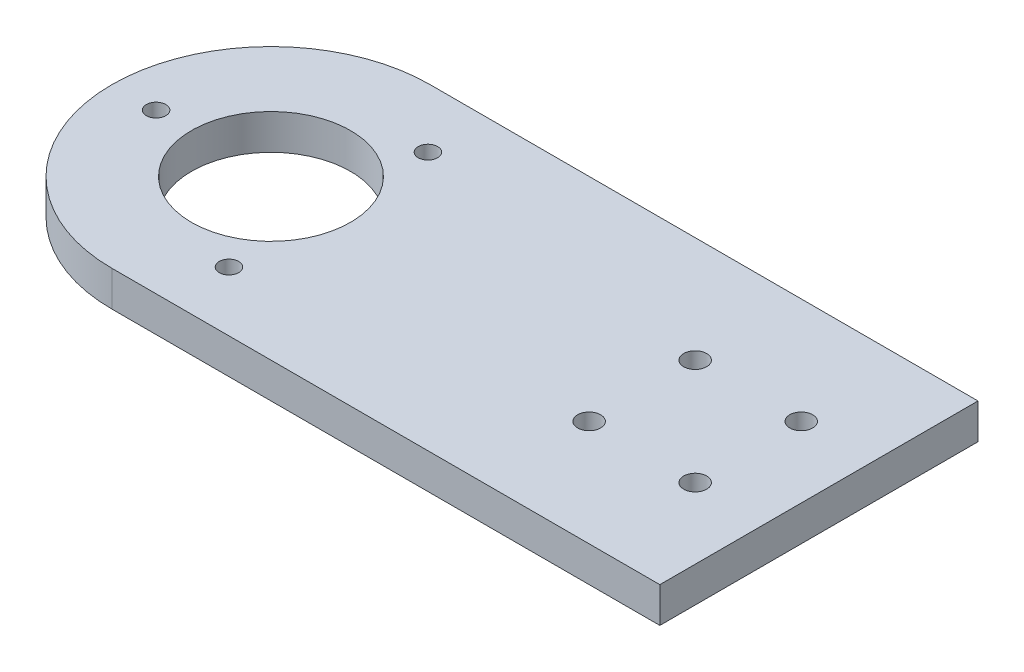
SolidWorks part; units mm, degrees
ref_plane "Front Plane" through (0, 0, 0) normal (0, 0, 1) x (1, 0, 0)
ref_plane "Top Plane" through (0, 0, 0) normal (0, 1, 0) x (1, 0, 0)
ref_plane "Right Plane" through (0, 0, 0) normal (1, 0, 0) x (0, 0, -1)
sketch "Sketch1" plane through (0, 0, 0) normal (0, 1, 0) x (1, 0, 0)
  line L0 (-55, 45) -> (100, 45)
  line L1 (-100, -45) -> (100, -45) construction
  line L2 (-100, -45) -> (-100, 45) construction
  line L3 (-100, 45) -> (100, 45) construction
  line L4 (100, -45) -> (100, 45) construction
  line L5 (0, 45) -> (0, -45) construction
  line L6 (-100, 0) -> (100, 0) construction
  line L7 (100, 45) -> (100, -45)
  line L8 (100, -45) -> (-55, -45)
  arc A1 (-55, 45) -> (-54.7588, -44.9994) centre (-55, 0) ccw
  point P0 (0, 0)
  dimension "D1" = 90
  dimension "D2" = 200
extrude "Boss-Extrude1" add sketch "Sketch1" along normal blind 10
sketch "Sketch2" plane through (0, 10, 0) normal (0, 1, 0) x (1, 0, 0)
  circle A0 centre (-55, 0) radius 32.5 construction
  circle A1 centre (-87.5, 0) radius 2.75
  circle A2 centre (-38.75, 28.1458) radius 2.75
  circle A3 centre (-38.75, -28.1458) radius 2.75
  circle A4 centre (-55, 0) radius 22.5
  point P11 (-55, 0)
  dimension "D1" = 65
  dimension "D2" = 5.5
  dimension "D4" = 45
  dimension "D3" = 3
extrude "Cut-Extrude1" cut sketch "Sketch2" against normal through all
sketch "Sketch3" plane through (0, 10, 0) normal (0, 1, 0) x (1, 0, 0)
  line L0 (100, 0) -> (-100, 0) construction
  line L1 (100, 45) -> (100, -45) construction
  line L3 (50, -15) -> (80, -15)
  line L4 (50, -15) -> (50, 15)
  line L5 (50, 15) -> (80, 15)
  line L6 (80, -15) -> (80, 15)
  line L7 (65, 15) -> (65, -15) construction
  line L8 (50, 0) -> (80, 0) construction
  arc A0 (-55, 45) -> (-55, -45) centre (-55, 0) ccw construction
  circle A1 centre (80, 15) radius 3.25
  circle A2 centre (50, 15) radius 3.25
  circle A3 centre (50, -15) radius 3.25
  circle A4 centre (80, -15) radius 3.25
  point P7 (65, 0)
  dimension "D1" = 6.5
  dimension "D2" = 30
  dimension "D3" = 30
  dimension "D4" = 20
extrude "Cut-Extrude2" cut sketch "Sketch3" against normal through all contours A2 | A1 | A4 | A3
